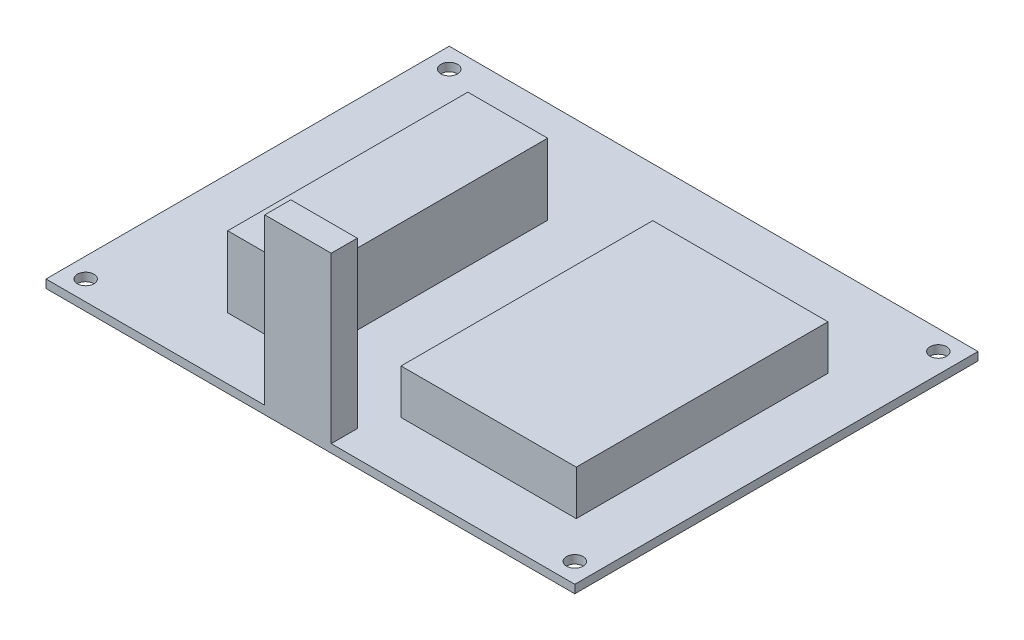
SolidWorks part; units mm, degrees
ref_plane "Front Plane" through (0, 0, 0) normal (0, 0, 1) x (1, 0, 0)
ref_plane "Top Plane" through (0, 0, 0) normal (0, 1, 0) x (1, 0, 0)
ref_plane "Right Plane" through (0, 0, 0) normal (1, 0, 0) x (0, 0, -1)
sketch "Sketch1" plane through (0, 0, 0) normal (0, 1, 0) x (1, 0, 0)
  line L1 (-97.371, 55.1184) -> (4.229, 55.1184)
  line L2 (-97.371, 55.1184) -> (-97.371, -22.3516)
  line L3 (-97.371, -22.3516) -> (4.229, -22.3516)
  line L4 (4.229, 55.1184) -> (4.229, -22.3516)
  dimension "D1" = 101.6
  dimension "D2" = 77.47
extrude "Boss-Extrude1" add sketch "Sketch1" along normal blind 1.5875
sketch "Sketch2" plane through (0, 1.5875, 0) normal (0, 1, 0) x (1, 0, 0)
  line L0 (-97.371, 55.1184) -> (-97.371, -22.3516) construction
  line L1 (-97.371, -22.3516) -> (4.229, -22.3516) construction
  circle A0 centre (-93.561, -18.5416) radius 1.6002
  circle A1 centre (-93.561, 51.3084) radius 1.6002
  circle A2 centre (0.419, 51.3084) radius 1.6002
  circle A3 centre (0.419, -18.5416) radius 1.6002
  point P0 (-93.561, -18.5416)
  point P1 (-93.561, 51.3084)
  point P2 (0.419, 51.3084)
  point P3 (0.419, -18.5416)
  dimension "D5" = 3.2004
  dimension "D6" = 3.2004
  dimension "D7" = 3.2004
  dimension "D8" = 3.2004
  dimension "D1" = 3.81
  dimension "D2" = 3.81
  dimension "D3" = 73.66
  dimension "D4" = 97.79
extrude "Cut-Extrude1" cut sketch "Sketch2" against normal blind 2.54
sketch "Sketch3" plane through (0, 0, 0) normal (0, 1, 0) x (1, 0, 0)
  line L0 (-97.371, -22.3516) -> (4.229, -22.3516) construction
  line L1 (-55.3419, -22.3516) -> (-42.5725, -22.3516)
  line L2 (-55.3419, -22.3516) -> (-55.3419, -17.3458)
  line L3 (-55.3419, -17.3458) -> (-42.5725, -17.3458)
  line L4 (-42.5725, -22.3516) -> (-42.5725, -17.3458)
extrude "Boss-Extrude2" add sketch "Sketch3" along normal blind 33.274
sketch "Sketch4" plane through (0, 0, 0) normal (0, 1, 0) x (1, 0, 0)
  line L1 (-40.2178, 37.0794) -> (-6.5531, 37.0794)
  line L2 (-40.2178, 37.0794) -> (-40.2178, -11.2894)
  line L3 (-40.2178, -11.2894) -> (-6.5531, -11.2894)
  line L4 (-6.5531, 37.0794) -> (-6.5531, -11.2894)
extrude "Boss-Extrude3" add sketch "Sketch4" along normal blind 10.16
sketch "Sketch5" plane through (0, 0, 0) normal (0, 1, 0) x (1, 0, 0)
  line L1 (-74.2857, 35.6137) -> (-58.9534, 35.6137)
  line L2 (-74.2857, 35.6137) -> (-74.2857, -10.5253)
  line L3 (-74.2857, -10.5253) -> (-58.9534, -10.5253)
  line L4 (-58.9534, 35.6137) -> (-58.9534, -10.5253)
extrude "Boss-Extrude4" add sketch "Sketch5" along normal blind 15.24
equation "\"D6@Sketch2\"=\"D5@Sketch2\""
equation "\"D7@Sketch2\"=\"D5@Sketch2\""
equation "\"D8@Sketch2\"=\"D5@Sketch2\""
